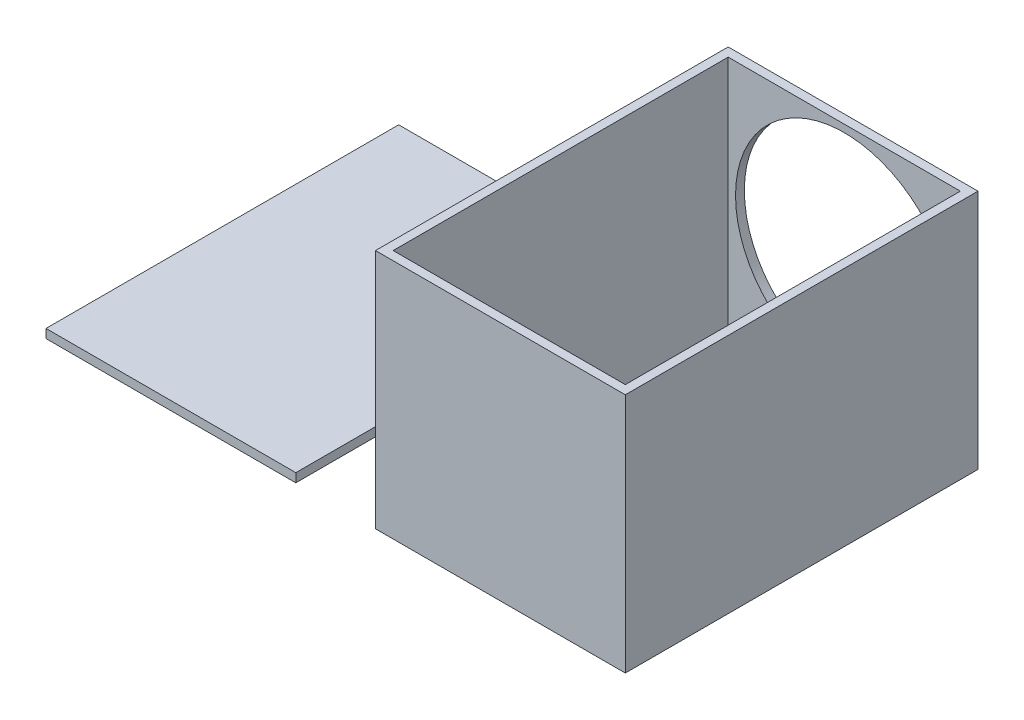
SolidWorks part; units mm, degrees
ref_plane "Front Plane" through (0, 0, 0) normal (0, 0, 1) x (1, 0, 0)
ref_plane "Top Plane" through (0, 0, 0) normal (0, 1, 0) x (1, 0, 0)
ref_plane "Right Plane" through (0, 0, 0) normal (1, 0, 0) x (0, 0, -1)
sketch "Sketch2" plane through (0, 0, 0) normal (0, 0, 1) x (1, 0, 0)
  line L1 (0, 82) -> (85, 82)
  line L2 (0, 82) -> (0, 0)
  line L3 (0, 0) -> (85, 0)
  line L4 (85, 82) -> (85, 0)
  line L5 (3, 82) -> (0, 82)
  line L6 (3, 82) -> (3, 0)
  line L7 (3, 0) -> (0, 0)
  line L8 (0, 82) -> (0, 0)
  circle A0 centre (42.5, 42.5) radius 37
  point P7 (0, 0)
  point P9 (0, 0)
  point P10 (0, 0)
  dimension "D3" = 74
  dimension "D1" = 85
  dimension "D2" = 82
extrude "Boss-Extrude1" add sketch "Sketch2" along normal blind 3 contours A0 | L1 L4 L3 L2
sketch "Sketch7" plane through (0, 0, 3) normal (0, 0, 1) x (1, 0, 0)
  line L0 (0, 0) -> (85, 0) construction
  line L1 (0, 82) -> (3, 82)
  line L2 (0, 82) -> (0, 0)
  line L3 (0, 0) -> (3, 0)
  line L4 (3, 82) -> (3, 0)
  dimension "D1" = 3
extrude "Boss-Extrude2" add sketch "Sketch7" along normal blind 117 contours L1 L4 L3 L2
sketch "Sketch8" plane through (0, 0, 3) normal (0, 0, 1) x (1, 0, 0)
  line L0 (85, 82) -> (85, 0) construction
  line L1 (3, 0) -> (85, 0)
  line L2 (3, 0) -> (3, 3)
  line L3 (3, 3) -> (85, 3)
  line L4 (85, 0) -> (85, 3)
  dimension "D1" = 3
extrude "Boss-Extrude3" add sketch "Sketch8" along normal blind 117 contours L3 L4 L1 L2
sketch "Sketch10" plane through (0, 0, 3) normal (0, 0, 1) x (1, 0, 0)
  line L2 (3, 3) -> (85, 3) construction
  line L3 (85, 82) -> (82, 82)
  line L4 (85, 82) -> (85, 3)
  line L5 (85, 3) -> (82, 3)
  line L6 (82, 82) -> (82, 3)
  dimension "D1" = 3
extrude "Boss-Extrude4" add sketch "Sketch10" along normal blind 117 contours L3 L6 L5 L4
sketch "Sketch11" plane through (0, 3, 0) normal (0, 1, 0) x (1, 0, 0)
  line L1 (3, -120) -> (82, -120)
  line L2 (3, -120) -> (3, -117)
  line L3 (3, -117) -> (82, -117)
  line L4 (82, -120) -> (82, -117)
  dimension "D1" = 79
  dimension "D2" = 3
extrude "Boss-Extrude5" add sketch "Sketch11" along normal blind 79 contours L1 L4 L3 L2
sketch "Sketch13" plane through (0, 0, 0) normal (0, 0, 1) x (1, 0, 0)
  line L1 (-27.1086, 3) -> (-112.1086, 3)
  line L2 (-27.1086, 3) -> (-27.1086, 0)
  line L3 (-27.1086, 0) -> (-112.1086, 0)
  line L4 (-112.1086, 3) -> (-112.1086, 0)
  dimension "D1" = 3
  dimension "D2" = 85
extrude "Boss-Extrude6" add sketch "Sketch13" along normal blind 120 separate body contours L4 L3 L2 L1
